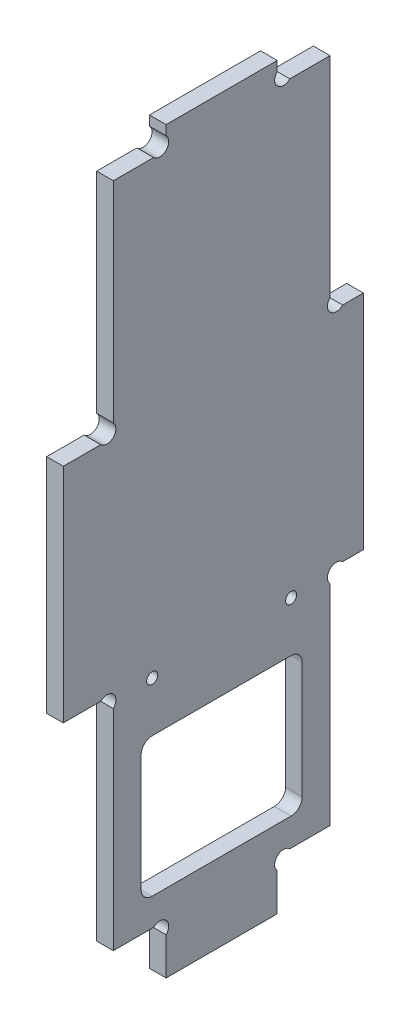
SolidWorks part; units mm, degrees
ref_plane "Plan de face" through (0, 0, 0) normal (0, 0, 1) x (1, 0, 0)
ref_plane "Plan de dessus" through (0, 0, 0) normal (0, 1, 0) x (1, 0, 0)
ref_plane "Plan de droite" through (0, 0, 0) normal (1, 0, 0) x (0, 0, -1)
sketch "Esquisse1" plane through (0, 0, 0) normal (1, 0, 0) x (0, 0, -1)
  line L13 (18.5, 6.7373) -> (18.5, 0)
  line L15 (16.2373, 9) -> (9, 9)
  line L17 (50.2627, 49) -> (54, 49)
  line L18 (6.7373, 49) -> (0, 49)
  line L19 (38.5, 6.7373) -> (38.5, 0)
  line L20 (50.2627, 89) -> (54, 89)
  line L21 (6.7373, 89) -> (0, 89)
  line L22 (18.5, 0) -> (38.5, 0)
  line L23 (40.7627, 9) -> (48, 9)
  line L24 (48, 9) -> (48, 46.7373)
  line L25 (9, 9) -> (9, 46.7373)
  line L26 (54, 89) -> (54, 49)
  line L27 (0, 49) -> (0, 89)
  line L29 (18.5, 131.2627) -> (18.5, 133)
  line L30 (38.5, 131.2627) -> (38.5, 133)
  line L31 (9, 91.2627) -> (9, 129)
  line L32 (9, 129) -> (16.2373, 129)
  line L33 (18.5, 133) -> (38.5, 133)
  line L34 (40.7627, 129) -> (48, 129)
  line L35 (48, 129) -> (48, 91.2627)
  arc A0 (50.2627, 49) -> (48, 46.7373) centre (49.1314, 47.8686) ccw
  arc A1 (9, 46.7373) -> (6.7373, 49) centre (7.8686, 47.8686) ccw
  arc A2 (18.5, 6.7373) -> (16.2373, 9) centre (17.3686, 7.8686) ccw
  arc A3 (38.5, 6.7373) -> (40.7627, 9) centre (39.6314, 7.8686) cw
  arc A4 (9, 91.2627) -> (6.7373, 89) centre (7.8686, 90.1314) cw
  arc A5 (50.2627, 89) -> (48, 91.2627) centre (49.1314, 90.1314) cw
  arc A6 (16.2373, 129) -> (18.5, 131.2627) centre (17.3686, 130.1314) ccw
  arc A7 (40.7627, 129) -> (38.5, 131.2627) centre (39.6314, 130.1314) cw
  point P1 (12.6186, 9)
  dimension "D14" = 1.1314
  dimension "D15" = 1.1314
  dimension "D17" = 1.1314
  dimension "D23" = 1.1314
  dimension "D10" = 1.6
  dimension "D1" = 6
  dimension "D2" = 9
  dimension "D3" = 9.5
  dimension "D4" = 9.5
  dimension "D5" = 9
  dimension "D6" = 40
  dimension "D7" = 40
  dimension "D8" = 40
  dimension "D9" = 4
  dimension "D11" = 1.1314
  dimension "D12" = 1.1314
  dimension "D13" = 1.1314
  dimension "D16" = 20
  dimension "D18" = 1.1314
  dimension "D19" = 1.1314
  dimension "D20" = 1.1314
  dimension "D21" = 1.1314
  dimension "D22" = 1.1314
  dimension "D24" = 3.7373
  dimension "D25" = 1.7373
  dimension "D26" = 1.1314
  dimension "D27" = 7.2373
  dimension "D28" = 1.1314
  dimension "D29" = 1.7373
  dimension "D30" = 20
  dimension "D31" = 39
  dimension "D32" = 39
extrude "Extrusion1" add sketch "Esquisse1" along normal blind 3
sketch "Esquisse2" plane through (3, 0, 0) normal (1, 0, 0) x (0, 0, -1)
  line L0 (9, 46.7373) -> (9, 9) construction
  line L1 (14, 14) -> (43, 14)
  line L2 (14, 14) -> (14, 39)
  line L3 (14, 39) -> (43, 39)
  line L4 (43, 14) -> (43, 39)
  line L5 (48, 9) -> (48, 46.7373) construction
  line L6 (9, 9) -> (16.2373, 9) construction
  dimension "D1" = 5
  dimension "D2" = 5
  dimension "D3" = 5
  dimension "D4" = 25
extrude "Enlèv. mat.-Extru.1" cut sketch "Esquisse2" against normal through all
fillet "Congé1" radius 2 4 edges at (1.5, 14, -43) (1.5, 14, -14) (1.5, 39, -14) (1.5, 39, -43)
sketch "Esquisse3" plane through (3, 0, 0) normal (1, 0, 0) x (0, 0, -1)
  line L0 (41, 39) -> (16, 39) construction
  line L1 (14, 37) -> (14, 16) construction
  line L2 (43, 16) -> (43, 37) construction
  circle A0 centre (16, 48) radius 1
  circle A1 centre (41, 48) radius 1
  point P4 (0, 0)
  point P9 (37.7878, 44)
  point P10 (0, 0)
  point P13 (0, 0)
  dimension "D2" = 2
  dimension "D1" = 9
  dimension "D3" = 2
  dimension "D4" = 2
  dimension "D5" = 25
extrude "Enlèv. mat.-Extru.2" cut sketch "Esquisse3" against normal through all
